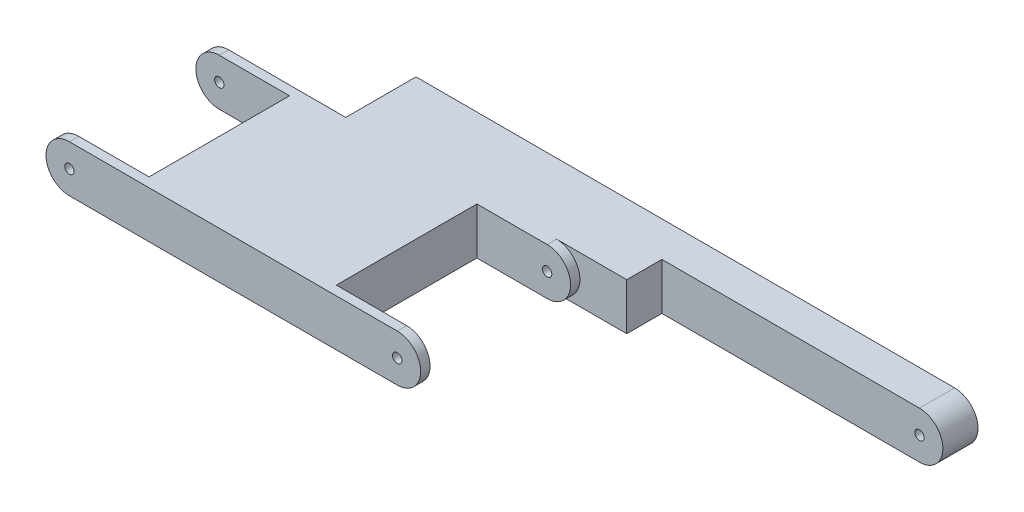
SolidWorks part; units mm, degrees
ref_plane "前基準面" through (0, 0, 0) normal (0, 0, 1) x (1, 0, 0)
ref_plane "上基準面" through (0, 0, 0) normal (0, 1, 0) x (1, 0, 0)
ref_plane "右基準面" through (0, 0, 0) normal (1, 0, 0) x (0, 0, -1)
sketch "草圖1" plane through (0, 0, 0) normal (0, 0, 1) x (1, 0, 0)
  line L0 (0, 47.1991) -> (0, -46.8309) construction
  line L1 (-71.1827, 0) -> (68.2665, 0) construction
  line L2 (-35, 0) -> (35, 0) construction
  line L3 (-35, 5) -> (35, 5)
  line L4 (-35, -5) -> (35, -5)
  arc A0 (-35, 5) -> (-35, -5) centre (-35, 0) ccw
  arc A1 (35, -5) -> (35, 5) centre (35, 0) ccw
  point P7 (0, 0)
  dimension "D2" = 5
  dimension "D1" = 70
extrude "填料-伸長1" add sketch "草圖1" along normal blind 34
sketch "草圖2" plane through (0, 0, 0) normal (0, 0, 1) x (1, 0, 0)
  line L0 (-45.1846, 0) -> (43.8227, 0) construction
  line L1 (0, 28.0802) -> (0, -27.5995) construction
  circle A0 centre (-35, 0) radius 1
  circle A1 centre (35, 0) radius 1
  dimension "D1" = 2
extrude "除料-伸長4" cut sketch "草圖2" against normal blind 30 and the other way through all
sketch "草圖3" plane through (0, 0, 0) normal (0, 1, 0) x (1, 0, 0)
  line L0 (35, 0) -> (-35, 0) construction
  line L1 (-40, -2) -> (-20, -2)
  line L2 (-40, -2) -> (-40, -32)
  line L3 (-40, -32) -> (-20, -32)
  line L4 (-20, -2) -> (-20, -32)
  line L5 (-35, -34) -> (-35, 0) construction
  line L6 (0, 16.8532) -> (0, -37.2241) construction
  line L7 (20, -2) -> (20, -32)
  line L8 (40, -32) -> (20, -32)
  line L9 (40, -2) -> (40, -32)
  line L10 (40, -2) -> (20, -2)
  dimension "D1" = 20
  dimension "D2" = 30
  dimension "D3" = 2
  dimension "D4" = 15
extrude "除料-伸長5" cut sketch "草圖3" against normal blind 30 and the other way blind 30
sketch "草圖4" plane through (0, 0, 0) normal (0, 0, 1) x (1, 0, 0)
  line L0 (0, 30.8378) -> (0, -29.7952) construction
  line L1 (-46.758, 0) -> (67.6106, 0) construction
  line L2 (35, 5) -> (-35, 5) construction
  line L3 (0, 5) -> (105, 5)
  line L4 (0, 5) -> (0, -5)
  line L5 (0, -5) -> (105, -5)
  line L6 (67.6106, 0) -> (119.1614, 0) construction
  arc A2 (105, -5) -> (105, 5) centre (105, 0) ccw
  dimension "D2" = 0
  dimension "D1" = 10
extrude "填料-伸長4" add sketch "草圖4" against normal blind 15
sketch "草圖5" plane through (0, 0, 0) normal (0, 0, 1) x (1, 0, 0)
  line L0 (132.2955, 0) -> (-55.3781, 0) construction
  line L1 (70, 38.422) -> (70, -46.2417)
  circle A0 centre (35, 0) radius 1
  circle A1 centre (105, 0) radius 1
  dimension "D2" = 2
  dimension "D1" = 35
extrude "除料-伸長7" cut sketch "草圖5" against normal through all contours A0 | A1
sketch "草圖6" plane through (0, 0, 0) normal (1, 0, 0) x (0, 0, -1)
  line L0 (23.7934, 0) -> (-11.2704, 0) construction
  line L1 (0, 16.6467) -> (0, -15.2206) construction
  line L3 (15, 5) -> (0, 5)
  line L4 (15, 5) -> (15, -5)
  line L5 (15, -5) -> (0, -5)
  line L6 (0, 5) -> (0, -5)
extrude "填料-伸長5" add sketch "草圖6" against normal blind 10
sketch "草圖7" plane through (0, 0, 0) normal (0, 1, 0) x (1, 0, 0)
  line L0 (105, 15) -> (-10, 15) construction
  line L1 (50, 7.5) -> (120, 7.5)
  line L2 (50, 7.5) -> (50, -2.5)
  line L3 (50, -2.5) -> (120, -2.5)
  line L4 (120, 7.5) -> (120, -2.5)
  line L5 (-10, 15) -> (-10, 0) construction
  dimension "D1" = 70
  dimension "D2" = 10
  dimension "D3" = 7.5
  dimension "D4" = 60
extrude "除料-伸長8" cut sketch "草圖7" against normal blind 10 and the other way blind 10
